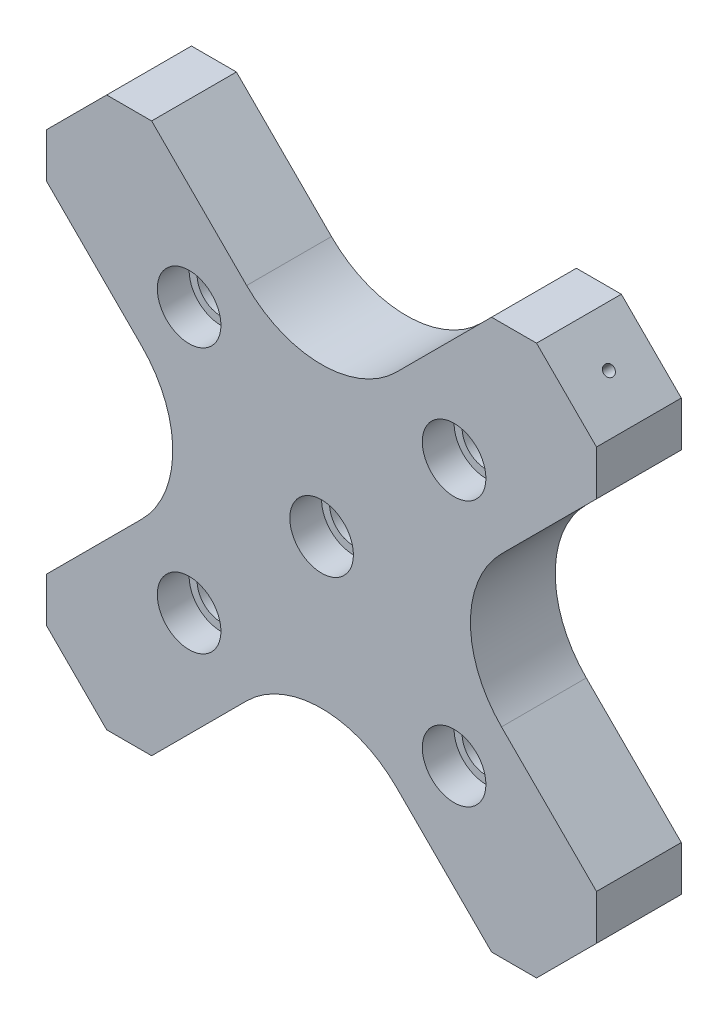
SolidWorks part; units mm, degrees
ref_plane "Plan de face" through (0, 0, 0) normal (0, 0, 1) x (1, 0, 0)
ref_plane "Plan de dessus" through (0, 0, 0) normal (0, 1, 0) x (1, 0, 0)
ref_plane "Plan de droite" through (0, 0, 0) normal (1, 0, 0) x (0, 0, -1)
sketch "Esquisse1" plane through (0, 0, 0) normal (0, 0, 1) x (1, 0, 0)
  line L0 (0, 0) -> (0, 26.5176) construction
  line L1 (0, 0) -> (37.6768, 0) construction
  line L2 (0, 0) -> (12.5, 12.5) construction
  line L3 (9.8995, 0) -> (25.935, 16.0355)
  line L4 (16.0355, 25.935) -> (20.2782, 25.935)
  line L5 (12.5, 12.5) -> (21.4775, 21.4775) construction
  line L6 (20.2782, 25.935) -> (25.935, 20.2782)
  line L7 (25.935, 16.0355) -> (25.935, 20.2782)
  line L8 (0, 9.8995) -> (16.0355, 25.935)
  line L9 (25.935, -16.0355) -> (25.935, -20.2782)
  line L10 (9.8995, 0) -> (25.935, -16.0355)
  line L11 (20.2782, -25.935) -> (25.935, -20.2782)
  line L12 (16.0355, -25.935) -> (20.2782, -25.935)
  line L13 (0, -9.8995) -> (16.0355, -25.935)
  line L14 (0, -9.8995) -> (-16.0355, -25.935)
  line L15 (-16.0355, -25.935) -> (-20.2782, -25.935)
  line L16 (-20.2782, -25.935) -> (-25.935, -20.2782)
  line L17 (-9.8995, 0) -> (-25.935, -16.0355)
  line L18 (-25.935, -16.0355) -> (-25.935, -20.2782)
  line L19 (0, 9.8995) -> (-16.0355, 25.935)
  line L20 (-25.935, 16.0355) -> (-25.935, 20.2782)
  line L21 (-20.2782, 25.935) -> (-25.935, 20.2782)
  line L22 (-16.0355, 25.935) -> (-20.2782, 25.935)
  line L23 (-9.8995, 0) -> (-25.935, 16.0355)
  line L24 (7.342, -2.5575) -> (0, -9.8995) construction
  line L25 (-7.342, -2.5575) -> (0, -9.8995) construction
  line L26 (-2.5575, -7.342) -> (-9.8995, 0) construction
  line L27 (-2.5575, 7.342) -> (-9.8995, 0) construction
  line L28 (-7.342, 2.5575) -> (0, 9.8995) construction
  line L29 (7.342, 2.5575) -> (0, 9.8995) construction
  line L30 (2.5575, 7.342) -> (9.8995, 0) construction
  line L31 (2.5575, -7.342) -> (9.8995, 0) construction
  circle A0 centre (12.5, 12.5) radius 2.25
  circle A1 centre (0, 0) radius 2.25
  circle A2 centre (12.5, -12.5) radius 2.25
  circle A3 centre (-12.5, 12.5) radius 2.25
  circle A4 centre (-12.5, -12.5) radius 2.25
  circle A5 centre (-12.5, -12.5) radius 2.25
  point P20 (19.2426, 10.7574)
  point P21 (0, 0)
  point P22 (0, 0)
  point P23 (4.3504, -4.1349)
  point P24 (24.4272, 15.9419)
  point P25 (19.2426, 10.7574)
  point P26 (23.1066, 23.1066)
  point P46 (-23.1066, 23.1066)
  dimension "D1" = 4.5
  dimension "D2" = 12.5
  dimension "D3" = 12.5
  dimension "D4" = 4.5
  dimension "D5" = 7
  dimension "D6" = 45
  dimension "D7" = 15
  dimension "D8" = 4
extrude "Boss.-Extru.1" add sketch "Esquisse1" along normal blind 8 contours L23 L17 L18 L16 L15 L14 L13 L12 L11 L9 L10 L3 L7 L6 L4 L8 L19 L22 L21 L20 A4 A2 A1 A0 A3
fillet "Congé1" radius 10 4 edges at (9.8995, 0, 4) (0, -9.8995, 4) (-9.8995, 0, 4) (0, 9.8995, 4)
sketch "Esquisse2" plane through (23.1066, 23.1066, 0) normal (0.7071, 0.7071, 0) x (0, 0, -1)
  line L0 (-8, 0) -> (0, 0) construction
  line L1 (-8, 4) -> (-8, -4) construction
  line L2 (-4, 4) -> (-4, -4) construction
  line L3 (-8, 4) -> (0, 4) construction
  line L4 (-8, -4) -> (0, -4) construction
  circle A0 centre (-4, 0) radius 0.5
  dimension "D1" = 1
extrude "Enlèv. mat.-Extru.1" cut sketch "Esquisse2" against normal blind 10
sketch "Esquisse3" plane through (0, 0, 8) normal (0, 0, 1) x (1, 0, 0)
  circle A0 centre (12.5, 12.5) radius 3
  circle A1 centre (0, 0) radius 3
  dimension "D1" = 6
  dimension "D2" = 6
extrude "Enlèv. mat.-Extru.2" cut sketch "Esquisse3" against normal blind 3
mirror "Symétrie1" about plane through (0, 0, 0) normal (0, 1, 0) of "Enlèv. mat.-Extru.2", "Enlèv. mat.-Extru.1"
mirror "Symétrie2" about plane through (0, 0, 0) normal (1, 0, 0) of "Symétrie1", "Enlèv. mat.-Extru.1", "Enlèv. mat.-Extru.2"
